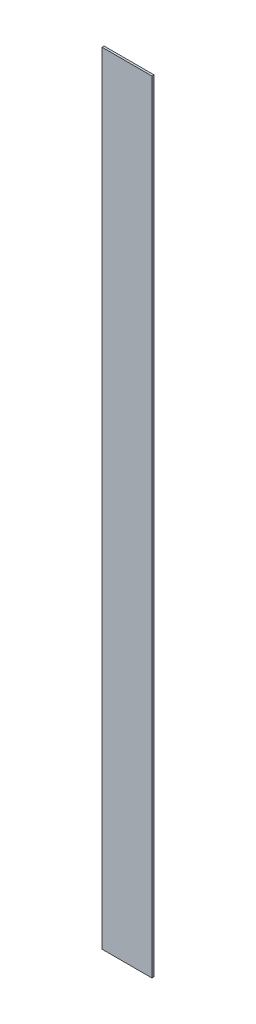
SolidWorks part; units mm, degrees
material "Cedar"
ref_plane "Front Plane" through (0, 0, 0) normal (0, 0, 1) x (1, 0, 0)
ref_plane "Top Plane" through (0, 0, 0) normal (0, 1, 0) x (1, 0, 0)
ref_plane "Right Plane" through (0, 0, 0) normal (1, 0, 0) x (0, 0, -1)
sketch "Sketch1" plane through (0, 0, 0) normal (0, 0, 1) x (1, 0, 0)
  line L0 (36.7474, -88.5393) -> (-59.2526, -88.5393)
  line L1 (-59.2526, -88.5393) -> (-59.2526, 1415.4607)
  line L2 (-59.2526, 1415.4607) -> (36.7474, 1415.4607)
  line L3 (36.7474, 1415.4607) -> (36.7474, -88.5393)
  line L4 (-131.0423, -88.5393) -> (181.4782, -88.5393) construction
  line L5 (-131.0423, 11.4607) -> (181.4782, 11.4607) construction
  line L6 (-131.0423, 111.4607) -> (181.4782, 111.4607) construction
  line L7 (-131.0423, 211.4607) -> (181.4782, 211.4607) construction
  line L8 (-131.0423, 311.4607) -> (181.4782, 311.4607) construction
  line L9 (-131.0423, 411.4607) -> (181.4782, 411.4607) construction
  line L10 (-131.0423, 511.4607) -> (181.4782, 511.4607) construction
  line L11 (-131.0423, 611.4607) -> (181.4782, 611.4607) construction
  line L12 (-131.0423, 711.4607) -> (181.4782, 711.4607) construction
  line L13 (-131.0423, 811.4607) -> (181.4782, 811.4607) construction
  line L14 (-131.0423, 911.4607) -> (181.4782, 911.4607) construction
  line L15 (-131.0423, 1011.4607) -> (181.4782, 1011.4607) construction
  line L16 (-131.0423, 1111.4607) -> (181.4782, 1111.4607) construction
  line L17 (-131.0423, 1211.4607) -> (181.4782, 1211.4607) construction
  line L18 (-131.0423, 1311.4607) -> (181.4782, 1311.4607) construction
  line L19 (-131.0423, 1411.4607) -> (181.4782, 1411.4607) construction
  dimension "D1" = 96
  dimension "D2" = 1504
  dimension "D3" = 16
extrude "Boss-Extrude1" add sketch "Sketch1" along normal blind 4 contours L3 L0 L1 L2
